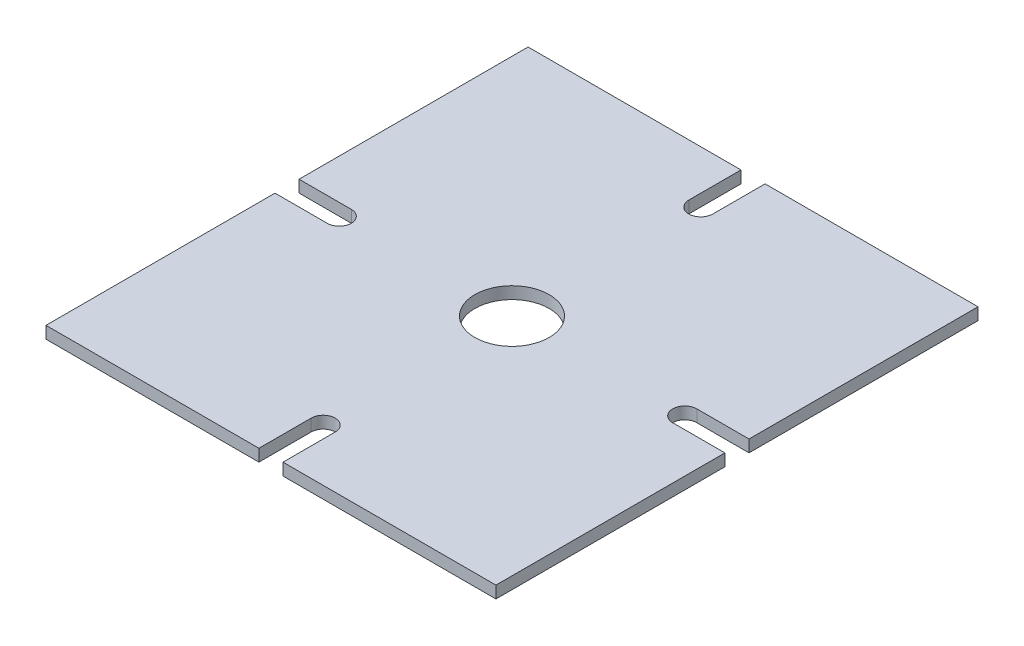
SolidWorks part; units mm, degrees
ref_plane "Front Plane" through (0, 0, 0) normal (0, 0, 1) x (1, 0, 0)
ref_plane "Top Plane" through (0, 0, 0) normal (0, 1, 0) x (1, 0, 0)
ref_plane "Right Plane" through (0, 0, 0) normal (1, 0, 0) x (0, 0, -1)
sketch "Sketch1" plane through (0, 0, 0) normal (0, 1, 0) x (1, 0, 0)
  line L1 (-56, -60) -> (56, -60)
  line L2 (-56, -60) -> (-56, 60)
  line L3 (-56, 60) -> (56, 60)
  line L4 (56, -60) -> (56, 60)
  line L5 (-56, -60) -> (56, 60) construction
  line L6 (-56, 60) -> (56, -60) construction
  point P0 (0, 0)
  dimension "D1" = 112
  dimension "D2" = 120
extrude "Boss-Extrude1" add sketch "Sketch1" along normal blind 3
sketch "Sketch2" plane through (0, 3, 0) normal (0, 1, 0) x (1, 0, 0)
  circle A0 centre (0, 0) radius 9.25
  dimension "D1" = 18.5
extrude "Cut-Extrude1" cut sketch "Sketch2" against normal blind 10
sketch "Sketch3" plane through (0, 3, 0) normal (0, 1, 0) x (1, 0, 0)
  line L0 (0, 60) -> (0, -60) construction
  line L1 (0, -60) -> (0, 60) construction
  line L2 (-56, 0) -> (56, 0) construction
  line L3 (-56, -60) -> (56, -60) construction
  line L4 (56, 60) -> (-56, 60) construction
  line L5 (56, -60) -> (56, 60) construction
  line L6 (-3, -60) -> (-3, -47)
  line L7 (3, -47) -> (3, -60)
  line L8 (-3, -60) -> (3, -60)
  line L9 (-3, 60) -> (3, 60)
  line L10 (3, 47) -> (3, 60)
  line L11 (-3, 60) -> (-3, 47)
  line L12 (56, 3) -> (43, 3)
  line L13 (43, -3) -> (56, -3)
  line L14 (56, 3) -> (56, -3)
  line L15 (-43, -3) -> (-56, -3)
  line L16 (-56, 3) -> (-43, 3)
  line L17 (-56, 3) -> (-56, -3)
  arc A0 (-3, -47) -> (3, -47) centre (0, -47) cw
  arc A1 (-3, 47) -> (3, 47) centre (0, 47) ccw
  arc A2 (43, 3) -> (43, -3) centre (43, 0) ccw
  arc A3 (-43, 3) -> (-43, -3) centre (-43, 0) cw
  point P26 (0, 0)
  dimension "D1" = 3
  dimension "D4" = 3
  dimension "D2" = 13
  dimension "D3" = 13
extrude "Cut-Extrude2" cut sketch "Sketch3" against normal blind 10
